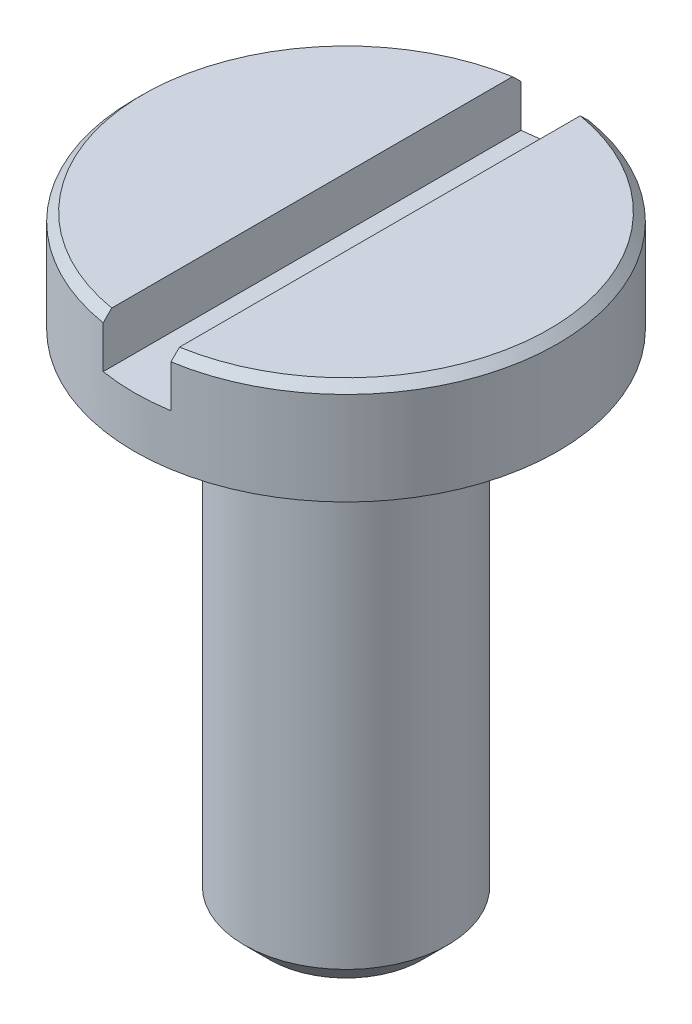
SolidWorks part; units mm, degrees
ref_plane "Alzado" through (0, 0, 0) normal (0, 0, 1) x (1, 0, 0)
ref_plane "Planta" through (0, 0, 0) normal (0, 1, 0) x (1, 0, 0)
ref_plane "Vista lateral" through (0, 0, 0) normal (1, 0, 0) x (0, 0, -1)
sketch "Sketch1" plane through (0, 0, 0) normal (0, 1, 0) x (1, 0, 0)
  circle A0 centre (0, 0) radius 1.25
  dimension "D1" = 2.5
extrude "Boss-Extrude1" add sketch "Sketch1" along normal blind 0.6
sketch "Sketch2" plane through (0, 0, 0) normal (0, 1, 0) x (1, 0, 0)
  circle A0 centre (0, 0) radius 0.6
  dimension "D1" = 1.2
extrude "Boss-Extrude2" add sketch "Sketch2" against normal blind 3
chamfer "Chamfer1" distance 0.05 angle 45 1 edges at (0, 0.6, 1.25)
chamfer "Chamfer2" distance 0.15 angle 45 1 edges at (0, -3, 0.6)
sketch "Sketch3" plane through (0, 0, 0) normal (0, 0, 1) x (1, 0, 0)
  line L0 (0, -1000) -> (0, 49000) construction
  line L1 (1.2, 0.6) -> (-1.2, 0.6) construction
  line L2 (-0.2, -999.9073) -> (-0.2, 49000.0927) construction
  line L3 (1.2, 0.6) -> (-1.2, 0.6) construction
  line L4 (-1000.8273, 0.3) -> (48999.1727, 0.3) construction
  line L5 (-0.2, 0.6) -> (0, 0.6)
  line L6 (-0.2, 0.6) -> (-0.2, 0.3)
  line L7 (0.2, 0.3) -> (0, 0.3)
  line L8 (-0.2, 0.3) -> (0, 0.3)
  line L9 (0.2, 0.6) -> (0.2, 0.3)
  line L10 (0.2, 0.6) -> (0, 0.6)
  dimension "D1" = 0.3
  dimension "D2" = 0.2
extrude "Cut-Extrude1" cut sketch "Sketch3" against normal through all both and the other way through all
